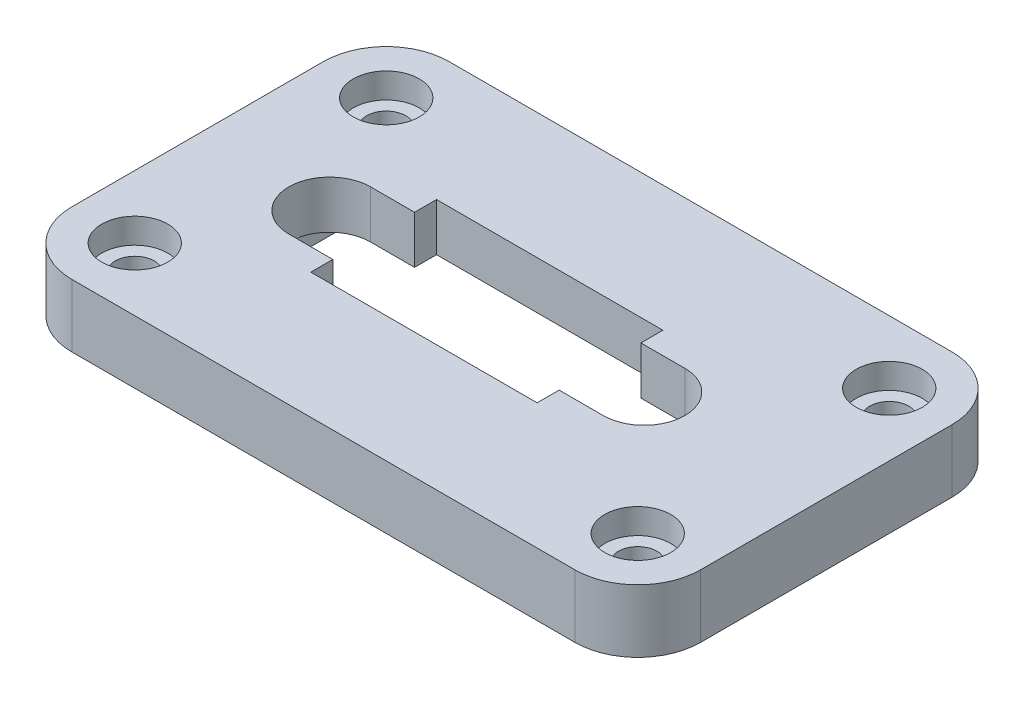
SolidWorks part; units mm, degrees
ref_plane "Front Plane" through (0, 0, 0) normal (0, 0, 1) x (1, 0, 0)
ref_plane "Top Plane" through (0, 0, 0) normal (0, 1, 0) x (1, 0, 0)
ref_plane "Right Plane" through (0, 0, 0) normal (1, 0, 0) x (0, 0, -1)
sketch "Sketch1" plane through (0, 0, 0) normal (0, 1, 0) x (1, 0, 0)
  line L0 (-2, -999.9458) -> (-2, 49000.0542) construction
  line L1 (-25, -15) -> (25, -15)
  line L2 (-25, -15) -> (-25, 15)
  line L3 (-25, 15) -> (25, 15)
  line L4 (25, -15) -> (25, 15)
  line L5 (-25, -15) -> (25, 15) construction
  line L6 (-25, 15) -> (25, -15) construction
  line L7 (-1000, 0) -> (49000, 0) construction
  line L8 (-14.5, -1000) -> (-14.5, 49000) construction
  line L9 (-11, -5) -> (7, -5)
  line L10 (-11, -5) -> (-11, 5)
  line L11 (-11, 5) -> (7, 5)
  line L12 (7, -5) -> (7, 5)
  line L13 (-11, -5) -> (7, 5) construction
  line L14 (-11, 5) -> (7, -5) construction
  line L15 (10.5, -1001.9507) -> (10.5, 48998.0493) construction
  line L16 (-14.5, 3.25) -> (-11, 3.25)
  line L17 (-14.5, -3.25) -> (-11, -3.25)
  line L18 (10.5, 3.25) -> (7, 3.25)
  line L19 (10.5, -3.25) -> (7, -3.25)
  line L20 (-1005.8997, 10) -> (48994.1003, 10) construction
  line L21 (-1006.3445, -10) -> (48993.6555, -10) construction
  line L22 (-20, -992.2102) -> (-20, 49007.7898) construction
  line L23 (20, -995.4415) -> (20, 49004.5585) construction
  circle A0 centre (-14.5, 0) radius 3.25
  circle A1 centre (10.5, 0) radius 3.25
  circle A2 centre (-20, 10) radius 1.55
  circle A3 centre (-20, -10) radius 1.55
  circle A4 centre (20, -10) radius 1.55
  circle A5 centre (20, 10) radius 1.55
  point P0 (0, 0)
  point P9 (-2, 0)
  dimension "D9" = 6.5
  dimension "D11" = 6.5
  dimension "D17" = 3.1
  dimension "D19" = 3.1
  dimension "D21" = 3.1
  dimension "D23" = 3.1
  dimension "D1" = 50
  dimension "D2" = 30
  dimension "D3" = 2
  dimension "D4" = 18
  dimension "D5" = 10
  dimension "D6" = 12.5
  dimension "D7" = 12.5
  dimension "D8" = 0
  dimension "D10" = 0
  dimension "D12" = 5
  dimension "D13" = 5
  dimension "D14" = 5
  dimension "D15" = 5
  dimension "D16" = 0
  dimension "D18" = 0
  dimension "D20" = 0
  dimension "D22" = 0
extrude "Boss-Extrude1" add sketch "Sketch1" along normal blind 5 contours L1 L4 L3 L2 A5 A4 A3 A2 A1 L19 L12 L9 L10 L17 A0 L16 L11 L18
sketch "Sketch2" plane through (0, 5, 0) normal (0, 1, 0) x (1, 0, 0)
  circle A0 centre (-20, 10) radius 2.625
  circle A1 centre (20, 10) radius 2.625
  circle A2 centre (20, -10) radius 2.625
  circle A3 centre (-20, -10) radius 2.625
  dimension "D1" = 5.25
  dimension "D2" = 5.25
  dimension "D3" = 5.25
  dimension "D4" = 5.25
extrude "Cut-Extrude1" cut sketch "Sketch2" against normal blind 2
sketch "Sketch3" plane through (0, 0, 0) normal (0, -1, 0) x (1, 0, 0)
  line L0 (-1000, 0) -> (49000, 0) construction
  line L1 (-2, -995) -> (-2, 49005) construction
  line L2 (-11, 5) -> (7, 5) construction
  line L4 (13.75, -6.5) -> (-17.75, -6.5)
  line L5 (13.75, -6.5) -> (13.75, 6.5)
  line L6 (13.75, 6.5) -> (-17.75, 6.5)
  line L7 (-17.75, -6.5) -> (-17.75, 6.5)
  line L8 (13.75, -6.5) -> (-17.75, 6.5) construction
  line L9 (13.75, 6.5) -> (-17.75, -6.5) construction
  point P4 (-2, 0)
  point P8 (-2, 5)
  dimension "D1" = 31.5
  dimension "D2" = 13
extrude "Cut-Extrude2" cut sketch "Sketch3" against normal blind 1.2
fillet "Fillet1" radius 5 4 edges at (25, 2.5, 15) (-25, 2.5, 15) (-25, 2.5, -15) (25, 2.5, -15)
